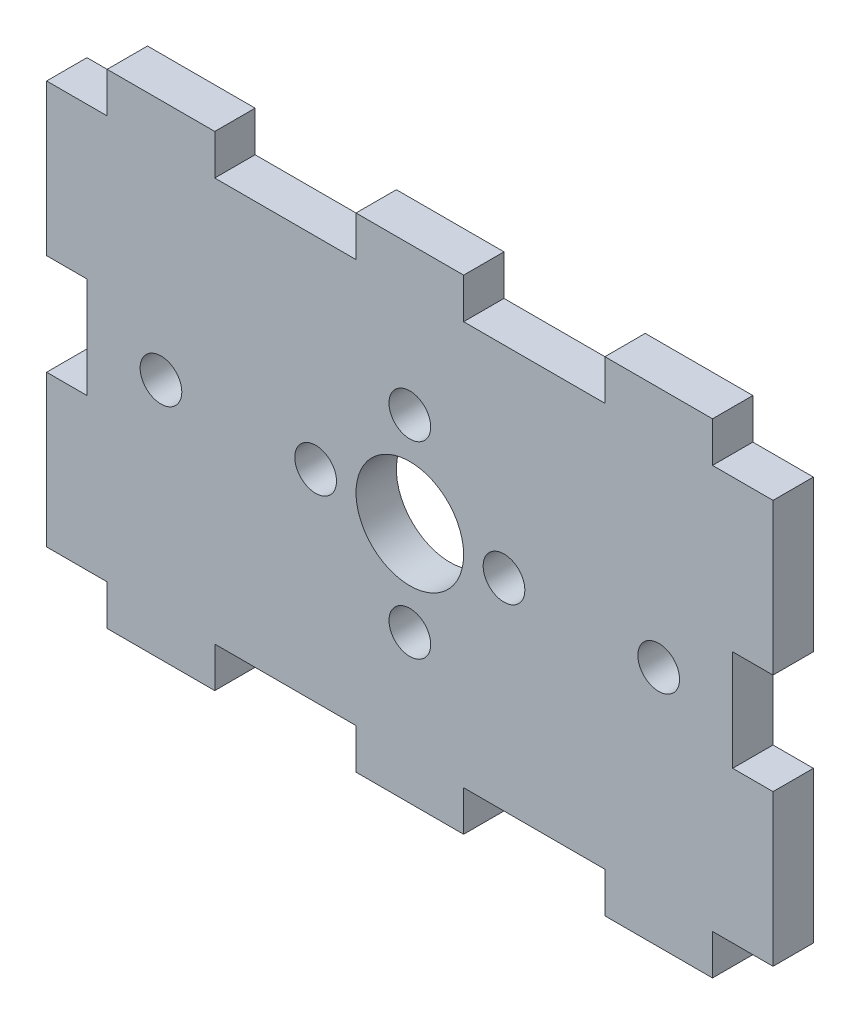
SolidWorks part; units mm, degrees
ref_plane "前视基准面" through (0, 0, 0) normal (0, 0, 1) x (1, 0, 0)
ref_plane "上视基准面" through (0, 0, 0) normal (0, 1, 0) x (1, 0, 0)
ref_plane "右视基准面" through (0, 0, 0) normal (1, 0, 0) x (0, 0, -1)
sketch "草图1" plane through (0, 0, 0) normal (0, 0, 1) x (1, 0, 0)
  line L0 (3214.8027, 1769.4192) -> (3225.3027, 1769.4192)
  line L1 (3233.3027, 1769.4192) -> (3243.8027, 1769.4192)
  line L2 (3256.3027, 1769.4192) -> (3256.3027, 1758.1692)
  line L3 (3256.3027, 1750.6692) -> (3256.3027, 1739.4192)
  line L4 (3243.8027, 1739.4192) -> (3233.3027, 1739.4192)
  line L5 (3225.3027, 1739.4192) -> (3214.8027, 1739.4192)
  line L6 (3202.3027, 1739.4192) -> (3202.3027, 1750.6692)
  line L7 (3202.3027, 1758.1692) -> (3202.3027, 1769.4192)
  line L8 (3214.8027, 1739.4192) -> (3214.8027, 1736.4192)
  line L9 (3214.8027, 1736.4192) -> (3206.8027, 1736.4192)
  line L10 (3206.8027, 1736.4192) -> (3206.8027, 1739.4192)
  line L11 (3233.3027, 1739.4192) -> (3233.3027, 1736.4192)
  line L12 (3233.3027, 1736.4192) -> (3225.3027, 1736.4192)
  line L13 (3225.3027, 1736.4192) -> (3225.3027, 1739.4192)
  line L14 (3251.8027, 1739.4192) -> (3251.8027, 1736.4192)
  line L15 (3251.8027, 1736.4192) -> (3243.8027, 1736.4192)
  line L16 (3243.8027, 1736.4192) -> (3243.8027, 1739.4192)
  line L17 (3214.8027, 1769.4192) -> (3214.8027, 1772.4192)
  line L18 (3214.8027, 1772.4192) -> (3206.8027, 1772.4192)
  line L19 (3206.8027, 1772.4192) -> (3206.8027, 1769.4192)
  line L20 (3233.3027, 1769.4192) -> (3233.3027, 1772.4192)
  line L21 (3233.3027, 1772.4192) -> (3225.3027, 1772.4192)
  line L22 (3225.3027, 1772.4192) -> (3225.3027, 1769.4192)
  line L23 (3251.8027, 1769.4192) -> (3251.8027, 1772.4192)
  line L24 (3251.8027, 1772.4192) -> (3243.8027, 1772.4192)
  line L25 (3243.8027, 1772.4192) -> (3243.8027, 1769.4192)
  line L26 (3202.3027, 1739.4192) -> (3206.8027, 1739.4192)
  line L27 (3251.8027, 1739.4192) -> (3256.3027, 1739.4192)
  line L28 (3202.3027, 1769.4192) -> (3206.8027, 1769.4192)
  line L29 (3251.8027, 1769.4192) -> (3256.3027, 1769.4192)
  line L30 (3202.3027, 1758.1692) -> (3205.3027, 1758.1692)
  line L31 (3205.3027, 1758.1692) -> (3205.3027, 1750.6692)
  line L32 (3205.3027, 1750.6692) -> (3202.3027, 1750.6692)
  line L33 (3256.3027, 1758.1692) -> (3253.3027, 1758.1692)
  line L34 (3253.3027, 1758.1692) -> (3253.3027, 1750.6692)
  line L35 (3253.3027, 1750.6692) -> (3256.3027, 1750.6692)
  circle A0 centre (3236.3027, 1754.4192) radius 1.55
  circle A1 centre (3229.3027, 1761.4192) radius 1.55
  circle A2 centre (3222.3027, 1754.4192) radius 1.55
  circle A3 centre (3229.3027, 1747.4192) radius 1.55
  circle A4 centre (3229.3027, 1754.4192) radius 4
  circle A5 centre (3247.8027, 1754.4192) radius 1.55
  circle A6 centre (3210.8027, 1754.4192) radius 1.55
extrude "凸台-拉伸1" add sketch "草图1" along normal blind 3
